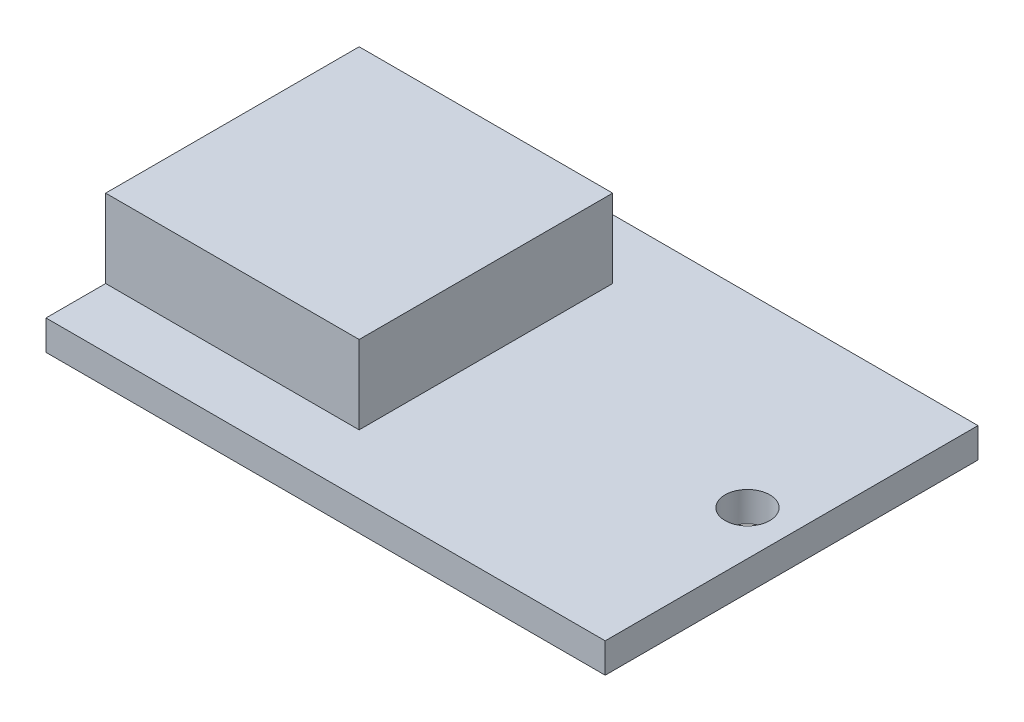
SolidWorks part; units mm, degrees
ref_plane "Front Plane" through (0, 0, 0) normal (0, 0, 1) x (1, 0, 0)
ref_plane "Top Plane" through (0, 0, 0) normal (0, 1, 0) x (1, 0, 0)
ref_plane "Right Plane" through (0, 0, 0) normal (1, 0, 0) x (0, 0, -1)
sketch "Sketch1" plane through (0, 0, 0) normal (0, 1, 0) x (1, 0, 0)
  line L0 (0, 0) -> (0, 25)
  line L1 (0, 25) -> (75, 25)
  line L2 (75, 25) -> (75, -25)
  line L3 (75, -25) -> (0, -25)
  line L4 (0, -25) -> (0, 0)
  dimension "D1" = 25
  dimension "D2" = 25
  dimension "D3" = 75
extrude "Boss-Extrude2" add sketch "Sketch1" along normal blind 4
sketch "Sketch7" plane through (0, 4, 0) normal (0, 1, 0) x (1, 0, 0)
  line L0 (0, 25) -> (0, -25) construction
  line L1 (0, 0) -> (0, 17)
  line L2 (0, 17) -> (34, 17)
  line L3 (34, 17) -> (34, -17)
  line L4 (34, -17) -> (0, -17)
  line L5 (0, -17) -> (0, 0)
  dimension "D1" = 8
  dimension "D2" = 34
  dimension "D3" = 34
extrude "Boss-Extrude4" add sketch "Sketch7" along normal blind 10.5
sketch "Sketch9" plane through (0, 4, 0) normal (0, 1, 0) x (1, 0, 0)
  circle A0 centre (69.079, 0) radius 3
  point P2 (0, 0)
extrude "Cut-Extrude1" cut sketch "Sketch9" against normal blind 10 contours A0
